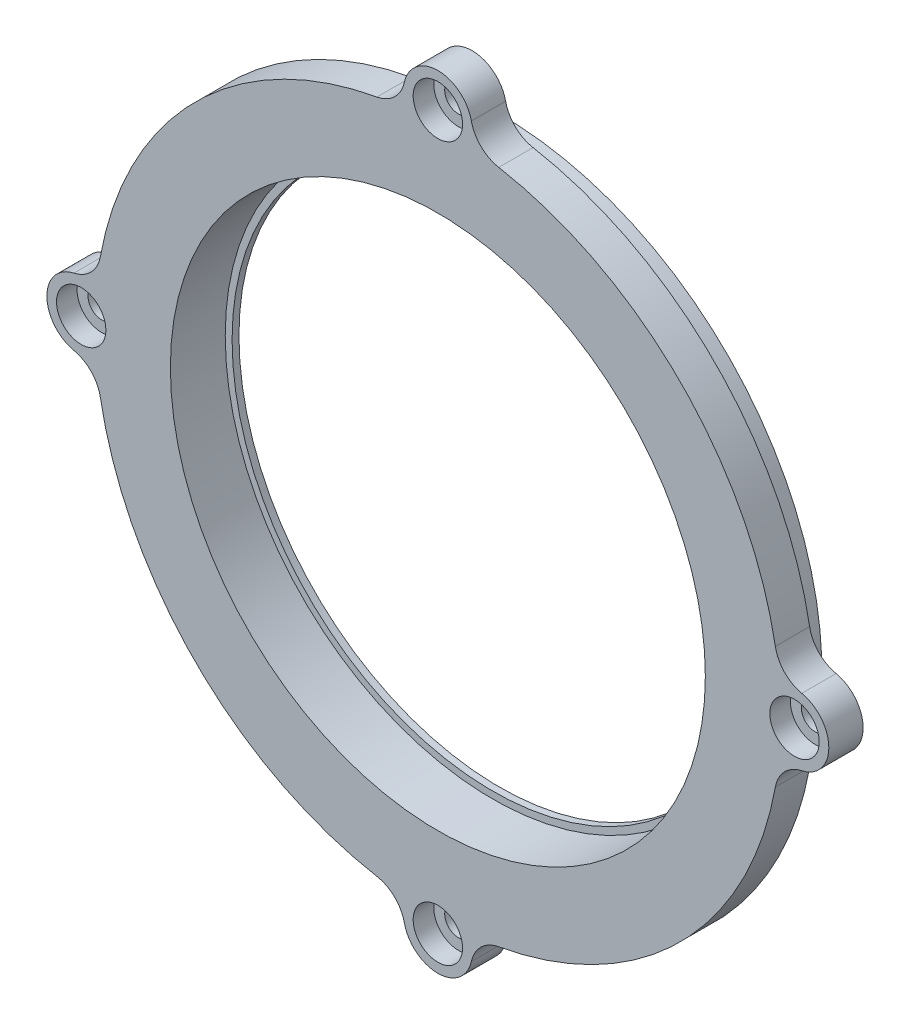
SolidWorks part; units mm, degrees
material "PET"
ref_plane "Front Plane" through (0, 0, 0) normal (0, 0, 1) x (1, 0, 0)
ref_plane "Top Plane" through (0, 0, 0) normal (0, 1, 0) x (1, 0, 0)
ref_plane "Right Plane" through (0, 0, 0) normal (1, 0, 0) x (0, 0, -1)
sketch "Sketch2" plane through (0, 0, 0) normal (0, 0, 1) x (1, 0, 0)
  circle A3 centre (0, 0) radius 50
  circle A4 centre (0, 0) radius 39
  dimension "D2" = 78
  dimension "D1" = 100
extrude "Boss-Extrude1" add sketch "Sketch2" along normal blind 5
sketch "Sketch3" plane through (0, 0, 0) normal (0, 0, -1) x (-1, 0, 0)
  circle A0 centre (-43, 0) radius 3
  circle A1 centre (0, 0) radius 39
  circle A2 centre (0, 0) radius 47
  circle A3 centre (0, 0) radius 50 construction
  circle A4 centre (-32.9399, 27.6399) radius 3
  circle A5 centre (-7.4669, 42.3467) radius 3
  circle A6 centre (21.5, 37.2391) radius 3
  circle A7 centre (40.4068, 14.7069) radius 3
  circle A8 centre (40.4068, -14.7069) radius 3
  circle A9 centre (21.5, -37.2391) radius 3
  circle A10 centre (-7.4669, -42.3467) radius 3
  circle A11 centre (-32.9399, -27.6399) radius 3
  point P27 (0, 0)
  dimension "D1" = 43
  dimension "D2" = 6
  dimension "D3" = 3
  dimension "D4" = 9
extrude "Boss-Extrude2" add sketch "Sketch3" along normal blind 4
sketch "Sketch4" plane through (0, 0, -4) normal (0, 0, -1) x (-1, 0, 0)
  circle A0 centre (0, 0) radius 39
  circle A1 centre (0, 0) radius 38
  dimension "D1" = 1
extrude "Boss-Extrude3" add sketch "Sketch4" against normal blind 1
sketch "Sketch6" plane through (0, 0, 5) normal (0, 0, 1) x (1, 0, 0)
  line L0 (0, 0) -> (52, 0) construction
  line L1 (0, 0) -> (0, 52) construction
  circle A0 centre (52, 0) radius 2
  circle A1 centre (52, 0) radius 5
  circle A2 centre (-52, 0) radius 5
  circle A3 centre (-52, 0) radius 2
  circle A4 centre (0, 52) radius 5
  circle A5 centre (0, 52) radius 2
  circle A8 centre (0, -52) radius 2
  circle A9 centre (0, -52) radius 5
  point P14 (50.7638, 0)
  dimension "D1" = 4
  dimension "D4" = 10
  dimension "D5" = 4
  dimension "D3" = 52
  dimension "D6" = 52
  dimension "D2" = 3
extrude "Boss-Extrude4" add sketch "Sketch6" against normal up to surface (5 mm away) up to face at (-47, 0, 0)
fillet "Fillet1" radius 5 8 edges at (49.7981, -4.489, 2.5) (49.7981, 4.489, 2.5) (4.489, 49.7981, 2.5) (-4.489, 49.7981, 2.5) (-49.7981, 4.489, 2.5) (-49.7981, -4.489, 2.5) (-4.489, -49.7981, 2.5) (4.489, -49.7981, 2.5)
sketch "Sketch7" plane through (0, 0, 5) normal (0, 0, 1) x (1, 0, 0)
  circle A0 centre (52, 0) radius 3.6
  circle A1 centre (0, 52) radius 3.6
  circle A2 centre (-52, 0) radius 3.6
  circle A3 centre (0, -52) radius 3.6
  dimension "D1" = 7.2
  dimension "D2" = 7.2
  dimension "D3" = 7.2
  dimension "D4" = 7.2
extrude "Cut-Extrude1" cut sketch "Sketch7" against normal blind 3
sketch "Sketch8" plane through (0, 0, -4) normal (0, 0, -1) x (-1, 0, 0)
  circle A1 centre (-32.9399, 27.6399) radius 3.15
  circle A2 centre (-43, 0) radius 3.15
  circle A3 centre (-43, 0) radius 3.15
  circle A4 centre (-7.4669, 42.3467) radius 3.15
  circle A5 centre (21.5, 37.2391) radius 3.15
  circle A6 centre (40.4068, 14.7069) radius 3.15
  circle A7 centre (40.4068, -14.7069) radius 3.15
  circle A8 centre (21.5, -37.2391) radius 3.15
  circle A9 centre (-7.4669, -42.3467) radius 3.15
  circle A10 centre (-32.9399, -27.6399) radius 3.15
  point P22 (0, 0)
  dimension "D1" = 0.15
  dimension "D2" = 9
extrude "Cut-Extrude2" cut sketch "Sketch8" against normal up to surface (4 mm away) up to face at (29.9399, 27.6399, 0)
